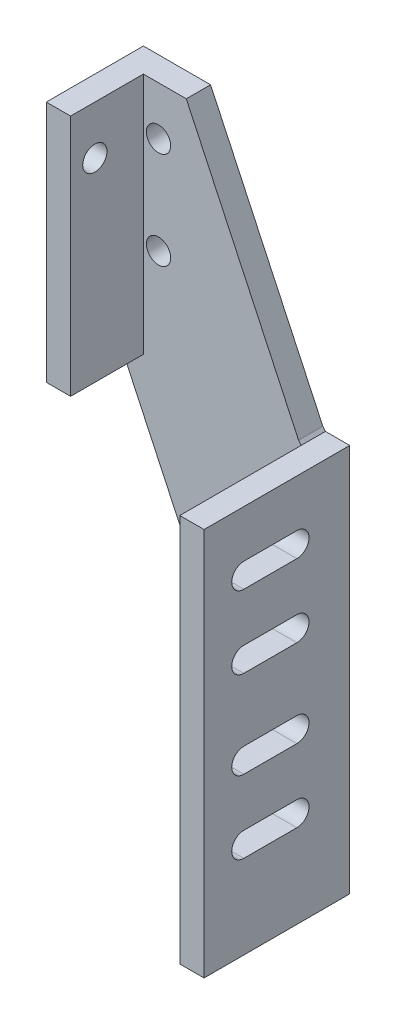
SolidWorks part; units mm, degrees
material "AISI 1018 Steel, Cold Rolled"
ref_plane "Front" through (0, 0, 0) normal (0, 0, 1) x (1, 0, 0)
ref_plane "Top" through (0, 0, 0) normal (0, 1, 0) x (1, 0, 0)
ref_plane "Right" through (0, 0, 0) normal (1, 0, 0) x (0, 0, -1)
sketch "Sketch1" plane through (0, 0, 0) normal (0, 0, 1) x (1, 0, 0)
  line L0 (1.3446, -204.8604) -> (1.3446, -1.6604)
  line L1 (-12.7, 0) -> (-71.4438, 125.3476)
  line L2 (-71.4438, 125.3476) -> (-106.5883, 125.3476)
  line L3 (-106.5883, 125.3476) -> (-106.5883, -1.6524)
  line L4 (-11.3554, -204.8604) -> (1.3446, -204.8604)
  line L5 (1.3446, -1.6604) -> (-11.3554, -1.6604)
  line L6 (-11.3554, -1.6604) -> (-12.7, 0)
  line L8 (-106.5883, -1.6524) -> (-11.3554, -204.8604)
extrude "Extrude1" add sketch "Sketch1" along normal blind 12.7
sketch "Sketch2" plane through (0, 0, 12.7) normal (0, 0, 1) x (1, 0, 0)
  line L1 (-106.5883, 125.3476) -> (-93.8883, 125.3476)
  line L2 (-106.5883, 125.3476) -> (-106.5883, -1.6524)
  line L3 (-106.5883, -1.6524) -> (-93.8883, -1.6524)
  line L4 (-93.8883, 125.3476) -> (-93.8883, -1.6524)
  dimension "D1" = 127
  dimension "D2" = 12.7
extrude "Extrude2" add sketch "Sketch2" along normal blind 38.1
sketch "Sketch3" plane through (0, 0, 12.7) normal (0, 0, 1) x (1, 0, 0)
  line L1 (1.3446, -204.8604) -> (-11.3554, -204.8604)
  line L2 (1.3446, -204.8604) -> (1.3446, -1.6604)
  line L3 (1.3446, -1.6604) -> (-11.3554, -1.6604)
  line L4 (-11.3554, -204.8604) -> (-11.3554, -1.6604)
extrude "Extrude3" add sketch "Sketch3" along normal blind 63.5
hole_wizard "1/2-20 Tapped Hole1" positions "3DSketch1" profile "Sketch4" tap size "1/2-20" standard "Ansi Inch" end condition through all
sketch3d "3DSketch1"
  line L0 (-106.5883, 125.3476, 50.8) -> (-106.5883, 125.3476, 0) construction
  line L3 (-106.5883, 125.3476, 0) -> (-106.5883, -1.6524, 0) construction
  point P0 (-106.5883, 99.9476, 38.1)
  dimension "D1" = 25.4
  dimension "D2" = 38.1
sketch "Sketch4" plane through (-106.5883, 99.9476, 38.1) normal (0, 1, 0) x (0, 0, 1)
  line L0 (0, 0) -> (0, 107.9329)
  line L1 (0, 107.9329) -> (6.35, 107.9329)
  line L2 (6.35, 107.9329) -> (6.35, 0)
  line L5 (6.35, 0) -> (0, 0)
  line L11 (0, -6.35) -> (0, 107.95) construction
  dimension "Thread Major Dia." = 12.7
  dimension "Thru Tap Drill Depth" = 107.9329
hole_wizard "1/2-20 Tapped Hole2" positions "3DSketch2" profile "Sketch5" tap size "1/2-20" standard "Ansi Inch" end condition through all
sketch3d "3DSketch2"
  line L0 (-71.4438, 125.3476, 0) -> (-106.5883, 125.3476, 0) construction
  line L1 (-106.5883, 125.3476, 0) -> (-106.5883, -1.6524, 0) construction
  point P0 (-85.9635, 99.9476, 0)
  point P1 (-85.9635, 49.1476, 0)
  dimension "D1" = 25.4
  dimension "D2" = 20.6248
  dimension "D3" = 20.6248
  dimension "D4" = 50.8
sketch "Sketch5" plane through (-85.9635, 99.9476, 0) normal (1, 0, 0) x (0, 1, 0)
  line L0 (0, 0) -> (0, 76.2)
  line L1 (0, 76.2) -> (6.35, 76.2)
  line L2 (6.35, 76.2) -> (6.35, 0)
  line L5 (6.35, 0) -> (0, 0)
  line L11 (0, -6.35) -> (0, 107.95) construction
  dimension "Thread Major Dia." = 12.7
  dimension "Thru Tap Drill Depth" = 76.2
sketch "Sketch6" plane through (1.3446, 0, 0) normal (1, 0, 0) x (0, 0, -1)
  line L0 (0, -204.8604) -> (0, -1.6604) construction
  line L1 (-55.372, -26.4254) -> (-27.6451, -26.4254)
  line L2 (-76.2, -1.6604) -> (0, -1.6604) construction
  line L3 (-27.6451, -39.1254) -> (-55.372, -39.1254)
  line L4 (-55.372, -64.5254) -> (-27.6451, -64.5254)
  line L5 (-55.372, -110.2454) -> (-27.6451, -110.2454)
  line L6 (-27.6451, -77.2254) -> (-55.372, -77.2254)
  line L7 (-27.6451, -122.9454) -> (-55.372, -122.9454)
  line L8 (-55.372, -148.3454) -> (-27.6451, -148.3454)
  line L9 (-27.6451, -161.0454) -> (-55.372, -161.0454)
  arc A0 (-55.372, -64.5254) -> (-55.372, -77.2254) centre (-55.372, -70.8754) ccw
  arc A1 (-27.6451, -77.2254) -> (-27.6451, -64.5254) centre (-27.6451, -70.8754) ccw
  arc A2 (-55.372, -26.4254) -> (-55.372, -39.1254) centre (-55.372, -32.7754) ccw
  arc A3 (-27.6451, -39.1254) -> (-27.6451, -26.4254) centre (-27.6451, -32.7754) ccw
  arc A4 (-55.372, -148.3454) -> (-55.372, -161.0454) centre (-55.372, -154.6954) ccw
  arc A5 (-27.6451, -161.0454) -> (-27.6451, -148.3454) centre (-27.6451, -154.6954) ccw
  arc A6 (-55.372, -110.2454) -> (-55.372, -122.9454) centre (-55.372, -116.5954) ccw
  arc A7 (-27.6451, -122.9454) -> (-27.6451, -110.2454) centre (-27.6451, -116.5954) ccw
  dimension "D1" = 55.372
  dimension "D2" = 69.215
extrude "Cut-Extrude1" cut sketch "Sketch6" against normal up to next
